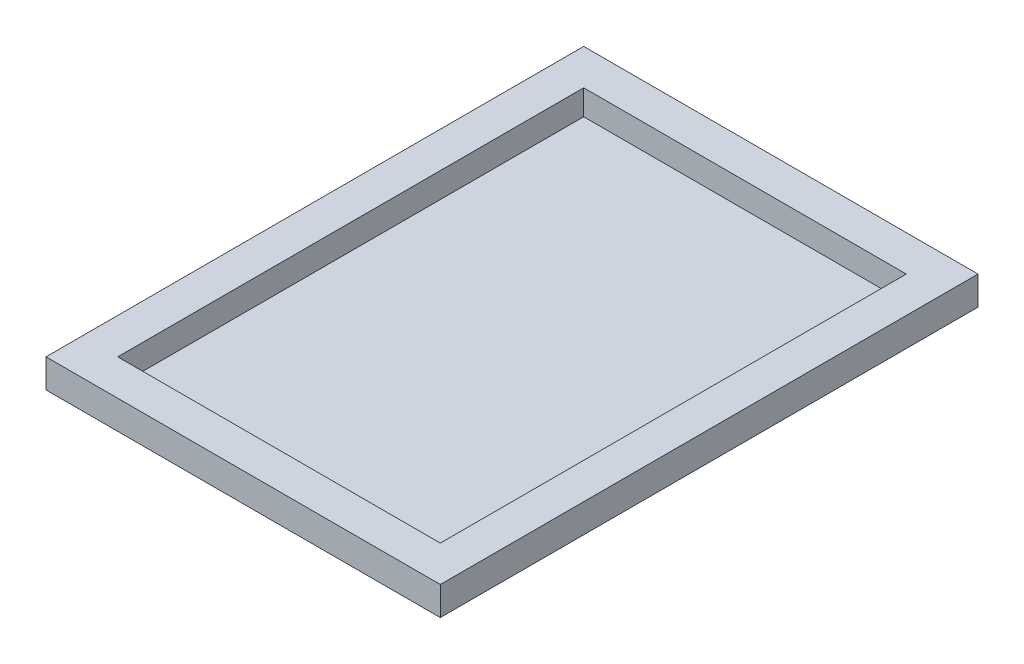
SolidWorks part; units mm, degrees
ref_plane "Přední rovina" through (0, 0, 0) normal (0, 0, 1) x (1, 0, 0)
ref_plane "Horní rovina" through (0, 0, 0) normal (0, 1, 0) x (1, 0, 0)
ref_plane "Pravá rovina" through (0, 0, 0) normal (1, 0, 0) x (0, 0, -1)
sketch "Skica1" plane through (0, 0, 0) normal (0, 1, 0) x (1, 0, 0)
  line L0 (-55, 75) -> (55, 75)
  line L1 (-45, 65) -> (45, 65)
  line L2 (-45, 65) -> (-45, -65)
  line L3 (-45, -65) -> (45, -65)
  line L4 (45, 65) -> (45, -65)
  line L5 (-45, 65) -> (45, -65) construction
  line L6 (-45, -65) -> (45, 65) construction
  line L7 (55, 75) -> (55, -75)
  line L8 (-55, -75) -> (55, -75)
  line L9 (-55, 75) -> (-55, -75)
  point P0 (0, 0)
  dimension "D1" = 130
  dimension "D2" = 90
  dimension "D3" = 10
extrude "Vysunout1" add sketch "Skica1" along normal blind 8
sketch "Skica2" plane through (0, 0, 0) normal (0, -1, 0) x (1, 0, 0)
  line L0 (45, -65) -> (-45, -65) construction
  line L1 (45, 65) -> (45, -65) construction
  line L2 (-45, -65) -> (-45, 65) construction
  line L3 (-45, 65) -> (45, 65) construction
  line L4 (45, -65) -> (-45, -65)
  line L5 (45, 65) -> (45, -65)
  line L6 (-45, -65) -> (-45, 65)
  line L7 (-45, 65) -> (45, 65)
extrude "Vysunout2" add sketch "Skica2" against normal blind 1
